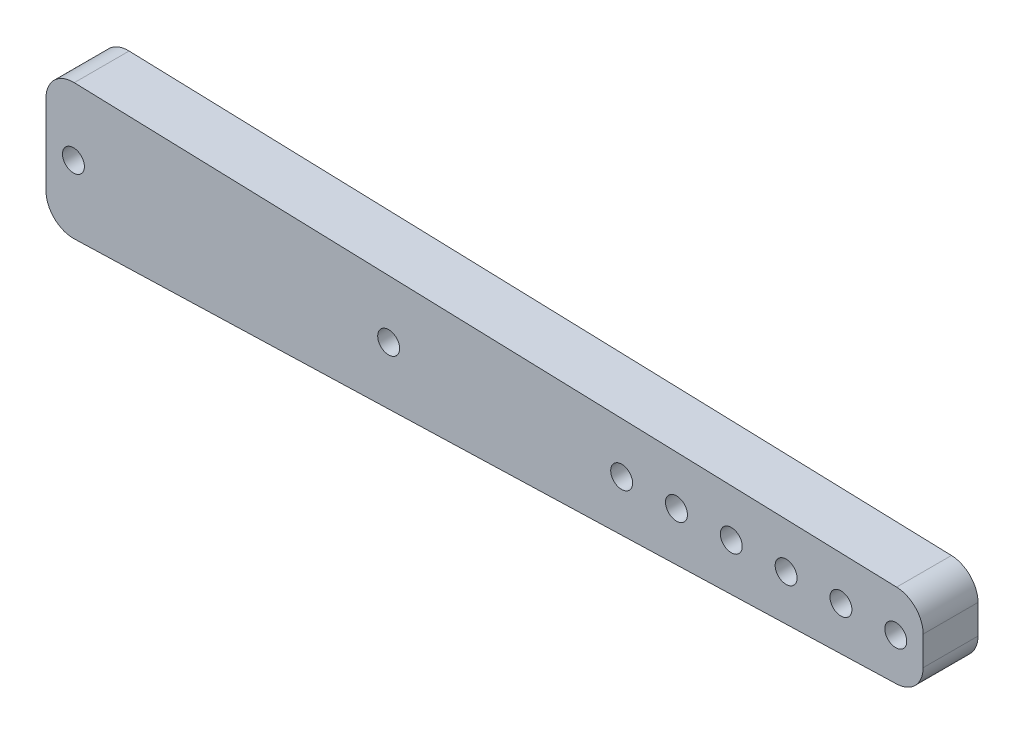
SolidWorks part; units mm, degrees
ref_plane "Front Plane" through (0, 0, 0) normal (0, 0, 1) x (1, 0, 0)
ref_plane "Top Plane" through (0, 0, 0) normal (0, 1, 0) x (1, 0, 0)
ref_plane "Right Plane" through (0, 0, 0) normal (1, 0, 0) x (0, 0, -1)
sketch "Sketch1" plane through (0, 0, 0) normal (0, 0, 1) x (1, 0, 0)
  line L0 (0, 0) -> (101.6, 3.175)
  line L1 (101.6, 3.175) -> (101.6, 12.7)
  line L2 (101.6, 12.7) -> (0, 15.875)
  line L3 (0, 15.875) -> (0, 0)
  line L4 (0, 7.9375) -> (101.6, 7.9375) construction
  dimension "D1" = 15.875
  dimension "D2" = 9.525
  dimension "D3" = 101.6
extrude "Boss-Extrude1" add sketch "Sketch1" along normal blind 6.35
sketch "Sketch2" plane through (0, 0, 6.35) normal (0, 0, 1) x (1, 0, 0)
  line L0 (0, 7.9375) -> (101.6, 7.9375) construction
  line L1 (0, 15.875) -> (0, 0) construction
  line L2 (101.6, 3.175) -> (101.6, 12.7) construction
  circle A0 centre (98.425, 7.9375) radius 1.27
  dimension "D1" = 2.54
  dimension "D2" = 3.175
extrude "Cut-Extrude1" cut sketch "Sketch2" against normal through all
sketch "Sketch3" plane through (0, 0, 6.35) normal (0, 0, 1) x (1, 0, 0)
  line L0 (0, 7.9375) -> (101.6, 7.9375) construction
  line L1 (0, 15.875) -> (0, 0) construction
  line L2 (101.6, 3.175) -> (101.6, 12.7) construction
pattern_linear "LPattern1" count 6 spacing 6.35 along (-1, 0, 0) of "Cut-Extrude1"
sketch "Sketch4" plane through (0, 0, 6.35) normal (0, 0, 1) x (1, 0, 0)
  line L0 (0, 7.9375) -> (101.6, 7.9375) construction
  line L1 (0, 15.875) -> (0, 0) construction
  circle A0 centre (3.175, 7.9375) radius 1.27
  circle A1 centre (39.6875, 7.9375) radius 1.27
  dimension "D1" = 2.54
  dimension "D3" = 36.5125
  dimension "D2" = 3.175
extrude "Cut-Extrude2" cut sketch "Sketch4" against normal through all
fillet "Fillet1" radius 3.175 4 edges at (101.6, 12.7, 3.175) (101.6, 3.175, 3.175) (0, 0, 3.175) (0, 15.875, 3.175)
